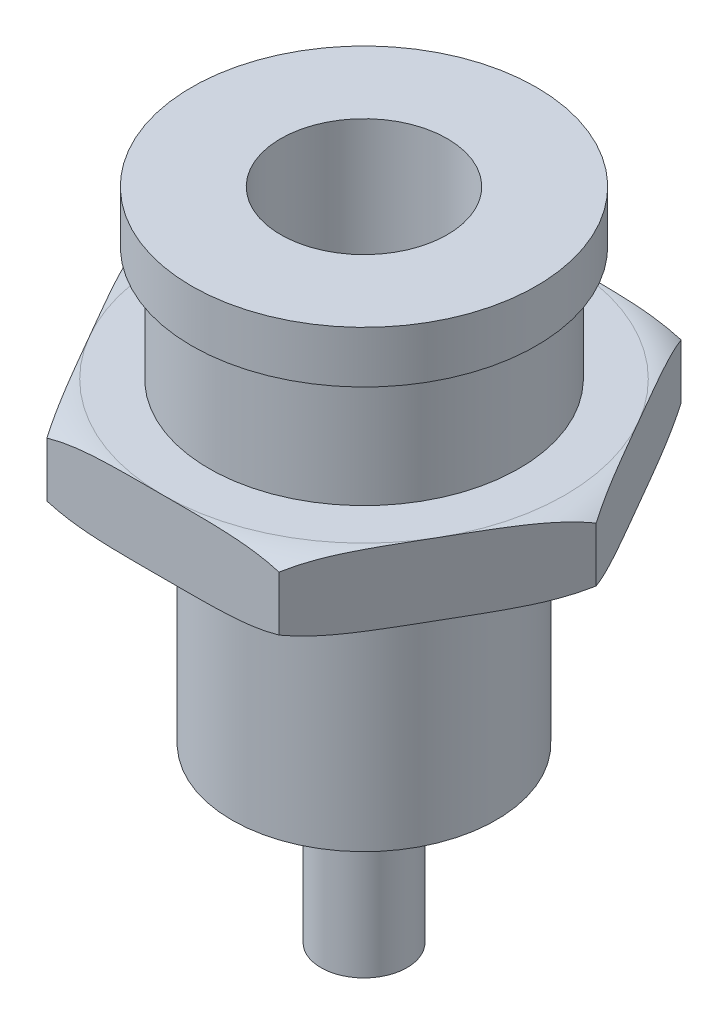
SolidWorks part; units mm, degrees
ref_plane "Front Plane" through (0, 0, 0) normal (0, 0, 1) x (1, 0, 0)
ref_plane "Top Plane" through (0, 0, 0) normal (0, 1, 0) x (1, 0, 0)
ref_plane "Right Plane" through (0, 0, 0) normal (1, 0, 0) x (0, 0, -1)
sketch "Sketch1" plane through (0, 0, 0) normal (0, 0, 1) x (1, 0, 0)
  line L0 (0, 0) -> (0, 12.8)
  line L1 (2.9, 22.8) -> (6, 22.8)
  line L2 (6, 22.8) -> (6, 21)
  line L3 (6, 21) -> (5.4, 21)
  line L4 (5.4, 21) -> (5.4, 16)
  line L5 (5.4, 16) -> (4.6, 16)
  line L6 (4.6, 16) -> (4.6, 6)
  line L7 (4.6, 6) -> (1.5, 6)
  line L8 (1.5, 6) -> (1.5, 0)
  line L9 (1.5, 0) -> (0, 0)
  line L10 (2.9, 22.8) -> (2.9, 12.8)
  line L11 (2.9, 12.8) -> (0, 12.8)
  dimension "D1" = 6
  dimension "D2" = 1.8
  dimension "D3" = 22.8
  dimension "D4" = 5.4
  dimension "D5" = 6.8
  dimension "D6" = 16.8
  dimension "D7" = 4.6
  dimension "D8" = 1.5
  dimension "D9" = 2.9
  dimension "D10" = 10
revolve "Revolve1" add sketch "Sketch1" angle 360 about L0
sketch "Sketch2" plane through (0, 21, 0) normal (0, -1, 0) x (1, 0, 0)
  line L1 (8.0829, 0) -> (4.0415, 7)
  line L2 (4.0415, 7) -> (-4.0415, 7)
  line L3 (-4.0415, 7) -> (-8.0829, 0)
  line L4 (-8.0829, 0) -> (-4.0415, -7)
  line L5 (-4.0415, -7) -> (4.0415, -7)
  line L6 (4.0415, -7) -> (8.0829, 0)
  circle A0 centre (0, 0) radius 7 construction
  dimension "D1" = 14
extrude "Boss-Extrude1" add sketch "Sketch2" along normal blind 2.5 from offset 4
sketch "Sketch3" plane through (0, 0, 0) normal (0, 0, 1) x (1, 0, 0)
  line L0 (-8.0829, 14.5) -> (-8.0829, 17) construction
  line L1 (-4.0415, 17) -> (-8.0829, 17) construction
  line L2 (-4.0415, 14.5) -> (-8.0829, 14.5) construction
  line L3 (-8.0829, 16.7) -> (-8.0829, 17)
  line L4 (-8.0829, 17) -> (-7, 17)
  line L5 (-8.0829, 14.8) -> (-8.0829, 14.5)
  line L6 (-8.0829, 14.5) -> (-7, 14.5)
  line L7 (4.0415, 17) -> (-4.0415, 17) construction
  line L8 (0, 14.5) -> (0, 17) construction
  line L9 (4.0415, 14.5) -> (-4.0415, 14.5) construction
  arc A0 (-8.0829, 16.7) -> (-7, 17) centre (-7, 14.8955) cw
  arc A1 (-8.0829, 14.8) -> (-7, 14.5) centre (-7, 16.6045) ccw
  point P19 (0, 17)
  dimension "D1" = 7
  dimension "D2" = 0.3
revolve "Cut-Revolve1" cut sketch "Sketch3" angle 360 about L8
